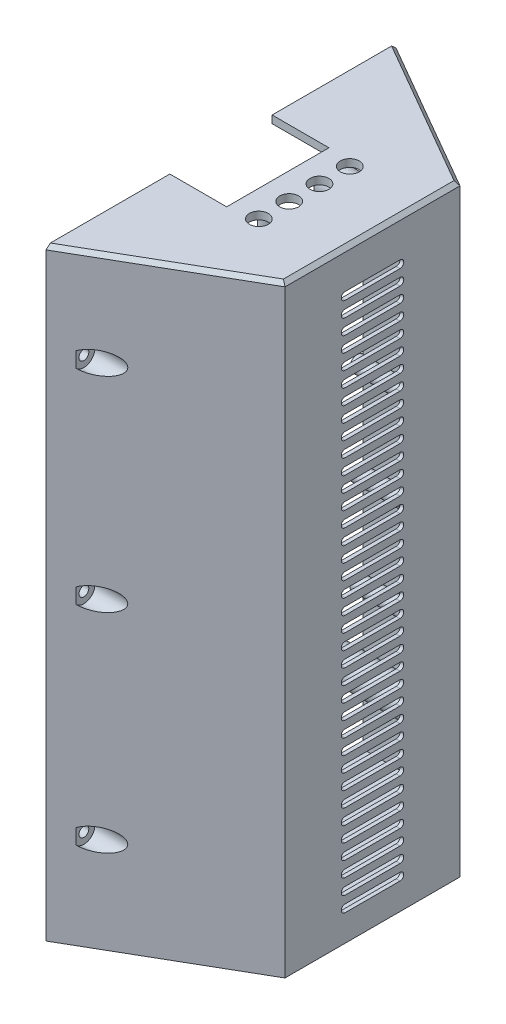
SolidWorks part; units mm, degrees
ref_plane "Front Plane" through (0, 0, 0) normal (0, 0, 1) x (1, 0, 0)
ref_plane "Top Plane" through (0, 0, 0) normal (0, 1, 0) x (1, 0, 0)
ref_plane "Right Plane" through (0, 0, 0) normal (1, 0, 0) x (0, 0, -1)
sketch "Sketch4" plane through (0, 0, 0) normal (0, 1, 0) x (1, 0, 0)
  line L0 (0, 46.188) -> (0, 45.0333)
  line L1 (0, -46.188) -> (40, -23.094)
  line L2 (40, -23.094) -> (40, 23.094)
  line L3 (40, 23.094) -> (0, 46.188)
  line L7 (0, -45.0333) -> (39, -22.5167)
  line L8 (39, -22.5167) -> (39, 22.5167)
  line L9 (39, 22.5167) -> (0, 45.0333)
  line L13 (0, -46.188) -> (0, -45.0333)
  line L15 (-40, -23.094) -> (0, -46.188) [skipped]
  line L16 (-39, -22.5167) -> (0, -45.0333) [skipped]
  line L17 (-39, 22.5167) -> (-39, -22.5167) [skipped]
  line L18 (-40, 23.094) -> (-40, -23.094) [skipped]
  line L19 (0, 45.0333) -> (-39, 22.5167) [skipped]
  line L20 (0, 46.188) -> (-40, 23.094) [skipped]
  dimension "D1" = 92.376
  dimension "D2" = 90.0666
extrude "Boss-Extrude5" add sketch "Sketch4" along normal blind 155
sketch "Sketch5" plane through (0, 0, 0) normal (0, -1, 0) x (1, 0, 0)
  line L0 (0, 46.188) -> (40, 23.094)
  line L1 (40, 23.094) -> (40, -23.094)
  line L2 (40, -23.094) -> (0, -46.188)
  line L3 (0, -46.188) -> (0, 46.188)
extrude "Boss-Extrude6" add sketch "Sketch5" along normal blind 2
sketch "Sketch6" plane through (0, 0, 0) normal (0, 1, 0) x (1, 0, 0)
  line L0 (0, -45.0333) -> (0, -37.5333)
  line L1 (0, -45.0333) -> (0, 45.0333) construction
  line L2 (0, 45.0333) -> (0, 37.5333)
  line L3 (0, -37.5333) -> (12.9904, -37.5333)
  line L4 (39, -22.5167) -> (0, -45.0333) construction
  line L5 (12.9904, -37.5333) -> (0, -45.0333)
  line L6 (0, 37.5333) -> (12.9904, 37.5333)
  line L7 (0, 45.0333) -> (39, 22.5167) construction
  line L8 (12.9904, 37.5333) -> (0, 45.0333)
  dimension "D1" = 7.5
  dimension "D2" = 7.5
extrude "Boss-Extrude7" add sketch "Sketch6" along normal blind 155
sketch "Sketch10" plane through (39, 0, 0) normal (-1, 0, 0) x (0, 0, 1)
  line L0 (-22.5167, 155) -> (22.5167, 155) construction
  line L1 (0, 155) -> (0, 0) construction
  line L2 (-22.5167, 0) -> (22.5167, 0) construction
  circle A0 centre (10, 115) radius 2
  circle A1 centre (-10, 115) radius 2
  circle A2 centre (-10, 115) radius 0.9
  circle A3 centre (10, 115) radius 0.9
  circle A4 centre (-10, 90) radius 2
  circle A5 centre (10, 90) radius 2
  circle A6 centre (-10, 90) radius 0.9
  circle A7 centre (10, 90) radius 0.9
  circle A8 centre (-10, 65) radius 2
  circle A9 centre (10, 65) radius 2
  circle A10 centre (-10, 65) radius 0.9
  circle A11 centre (10, 65) radius 0.9
  point P2 (0, 155)
  dimension "D1" = 4
  dimension "D2" = 40
  dimension "D3" = 10
  dimension "D4" = 4
  dimension "D5" = 10
  dimension "D6" = 40
  dimension "D7" = 1.8
  dimension "D8" = 1.8
  dimension "D9" = 4
  dimension "D10" = 4
  dimension "D11" = 25
  dimension "D12" = 25
  dimension "D13" = 10
  dimension "D14" = 10
  dimension "D15" = 1.8
  dimension "D16" = 1.8
  dimension "D17" = 4
  dimension "D18" = 4
  dimension "D19" = 10
  dimension "D20" = 10
  dimension "D21" = 25
  dimension "D22" = 25
  dimension "D23" = 1.8
  dimension "D24" = 1.8
extrude "Boss-Extrude9" add sketch "Sketch10" along normal blind 13
sketch "Sketch11" plane through (39, 0, 0) normal (-1, 0, 0) x (0, 0, 1)
  line L0 (-22.5167, 155) -> (22.5167, 155) construction
  line L1 (-7.25, 147) -> (0, 147)
  line L2 (0, 155) -> (0, 0) construction
  line L3 (-22.5167, 0) -> (22.5167, 0) construction
  line L4 (-7.25, 145) -> (0, 145)
  line L5 (0, 147) -> (7.25, 147)
  line L6 (7.25, 145) -> (0, 145)
  arc A0 (-7.25, 147) -> (-7.25, 145) centre (-7.25, 146) ccw
  arc A1 (7.25, 147) -> (7.25, 145) centre (7.25, 146) cw
  dimension "D1" = 7.25
  dimension "D2" = 7.25
  dimension "D3" = 7.25
  dimension "D4" = 8
  dimension "D6" = 7.25
  dimension "D5" = 2
extrude "Cut-Extrude1" cut sketch "Sketch11" against normal blind 2
pattern_linear "LPattern1" count 36 spacing 4 along (0, -1, 0) of "Cut-Extrude1"
sketch "Sketch12" plane through (0, 155, 0) normal (0, 1, 0) x (1, 0, 0)
  line L0 (0, 46.188) -> (40, 23.094)
  line L1 (40, 23.094) -> (40, -23.094)
  line L2 (40, -23.094) -> (0, -46.188)
  line L3 (0, -46.188) -> (0, 46.188)
extrude "Boss-Extrude10" add sketch "Sketch12" along normal blind 2
chamfer "Chamfer2" distance 1 angle 45 3 edges at (20, 157, -34.641) (40, 157, 0) (20, 157, 34.641)
sketch "Sketch16" plane through (0, 0, 0) normal (-1, 0, 0) x (0, 0, 1)
  line L0 (-37.5333, 155) -> (37.5333, 155) construction
  line L1 (0, 155) -> (0, 0) construction
  circle A0 centre (-28.5, 135) radius 4
  circle A1 centre (22.5, 135) radius 4
  circle A2 centre (23.5, 36.5) radius 4
  circle A3 centre (-23.5, 31) radius 4
  dimension "D1" = 8
  dimension "D2" = 8
  dimension "D3" = 28.5
  dimension "D7" = 8
  dimension "D8" = 8
  dimension "D9" = 104
  dimension "D10" = 98.5
  dimension "D12" = 23.5
  dimension "D4" = 22.5
  dimension "D5" = 20
  dimension "D6" = 20
  dimension "D11" = 23.5
extrude "Boss-Extrude12" add sketch "Sketch16" against normal up to next separate body
sketch "Sketch17" plane through (0, 0, 0) normal (-1, 0, 0) x (0, 0, 1)
  circle A0 centre (-23.5, 31) radius 1.3
  dimension "D1" = 2.6
extrude "Cut-Extrude2" cut sketch "Sketch17" against normal blind 10
sketch "Sketch18" plane through (0, 0, 0) normal (-1, 0, 0) x (0, 0, 1)
  circle A0 centre (23.5, 36.5) radius 1.3
  dimension "D1" = 2.6
extrude "Cut-Extrude3" cut sketch "Sketch18" against normal blind 10
sketch "Sketch19" plane through (0, 0, 0) normal (-1, 0, 0) x (0, 0, 1)
  circle A0 centre (-28.5, 135) radius 1.3
  dimension "D1" = 2.6
extrude "Cut-Extrude4" cut sketch "Sketch19" against normal blind 10
sketch "Sketch20" plane through (0, 0, 0) normal (-1, 0, 0) x (0, 0, 1)
  circle A0 centre (22.5, 135) radius 1.3
  dimension "D1" = 2.6
extrude "Cut-Extrude5" cut sketch "Sketch20" against normal blind 10
sketch "Sketch21" plane through (0, 157, 0) normal (0, 1, 0) x (1, 0, 0)
  line L3 (-15, 13.5) -> (15, 13.5)
  line L4 (-15, 13.5) -> (-15, -13.5)
  line L5 (-15, -13.5) -> (15, -13.5)
  line L6 (15, 13.5) -> (15, -13.5)
  line L7 (-15, 13.5) -> (15, -13.5) construction
  line L8 (-15, -13.5) -> (15, 13.5) construction
  dimension "D1" = 30
  dimension "D2" = 27
extrude "Cut-Extrude6" cut sketch "Sketch21" against normal blind 10
sketch "Sketch22" plane through (0, 155, 0) normal (0, -1, 0) x (1, 0, 0)
  line L1 (0, -13.5) -> (15, -13.5) construction
  line L2 (15, -13.5) -> (15, 13.5) construction
  line L3 (15, 13.5) -> (0, 13.5) construction
  circle A0 centre (8, -24.5) radius 2
  circle A1 centre (8, -24.5) radius 0.9
  circle A2 centre (18, 5.5) radius 2
  circle A3 centre (18, 5.5) radius 0.9
  dimension "D1" = 4
  dimension "D2" = 11
  dimension "D4" = 1.8
  dimension "D5" = 4
  dimension "D8" = 1.8
  dimension "D3" = 7
  dimension "D6" = 3
  dimension "D7" = 8
extrude "Boss-Extrude13" add sketch "Sketch22" along normal blind 10
sketch "Sketch23" plane through (0, 0, 0) normal (-1, 0, 0) x (0, 0, 1)
  line L0 (13.5, 157) -> (45.0333, 157) construction
  line L1 (46.188, 156) -> (46.188, -2) construction
  line L2 (-45.0333, 157) -> (-13.5, 157) construction
  line L3 (-46.188, 156) -> (-46.188, -2) construction
  line L4 (46.188, -2) -> (-46.188, -2) construction
  circle A0 centre (-41.188, 132) radius 1.3
  circle A1 centre (41.188, 132) radius 1.3
  circle A2 centre (-41.188, 78) radius 1.3
  circle A3 centre (41.188, 78) radius 1.3
  circle A4 centre (41.188, 23) radius 1.3
  circle A5 centre (-41.188, 23) radius 1.3
  dimension "D1" = 2.6
  dimension "D2" = 2.6
  dimension "D3" = 2.6
  dimension "D4" = 2.6
  dimension "D5" = 2.6
  dimension "D6" = 2.6
  dimension "D8" = 5
  dimension "D12" = 79
  dimension "D13" = 25
  dimension "D14" = 5
  dimension "D15" = 5
  dimension "D16" = 25
  dimension "D17" = 5
  dimension "D18" = 79
  dimension "D7" = 25
  dimension "D9" = 25
  dimension "D10" = 5
  dimension "D11" = 5
extrude "Cut-Extrude7" cut sketch "Sketch23" against normal blind 35
sketch "Sketch25" plane through (0, 157, 0) normal (0, 1, 0) x (1, 0, 0)
  line L1 (0, 0) -> (39, 0) construction
  line L2 (39, -22.5167) -> (39, 22.5167) construction
  line L3 (15, -13.5) -> (15, 13.5) construction
  circle A0 centre (22, 12) radius 2.5
  circle A1 centre (22, 4) radius 2.5
  circle A2 centre (22, -4) radius 2.5
  circle A3 centre (22, -12) radius 2.5
  dimension "D1" = 5
  dimension "D2" = 5
  dimension "D3" = 5
  dimension "D4" = 5
  dimension "D5" = 7
  dimension "D6" = 7
  dimension "D7" = 7
  dimension "D8" = 7
  dimension "D9" = 8
  dimension "D10" = 8
  dimension "D11" = 8
  dimension "D12" = 4
extrude "Cut-Extrude9" cut sketch "Sketch25" against normal blind 2
ref_plane "Plane1" through (5, 0, 0) normal (-1, 0, 0) x (0, 0, 1)
sketch "Sketch29" plane through (5, 0, 0) normal (-1, 0, 0) x (0, 0, 1)
  circle A0 centre (-41.188, 132) radius 2.9
  circle A1 centre (-41.188, 23) radius 2.9
  circle A2 centre (41.188, 23) radius 2.9
  circle A3 centre (41.188, 78) radius 2.9
  circle A4 centre (41.188, 132) radius 2.9
  circle A5 centre (-41.188, 78) radius 2.9
  dimension "D1" = 5.8
  dimension "D2" = 5.8
  dimension "D3" = 5.8
  dimension "D4" = 5.8
  dimension "D5" = 5.8
  dimension "D6" = 5.8
extrude "Cut-Extrude10" cut sketch "Sketch29" against normal blind 10
